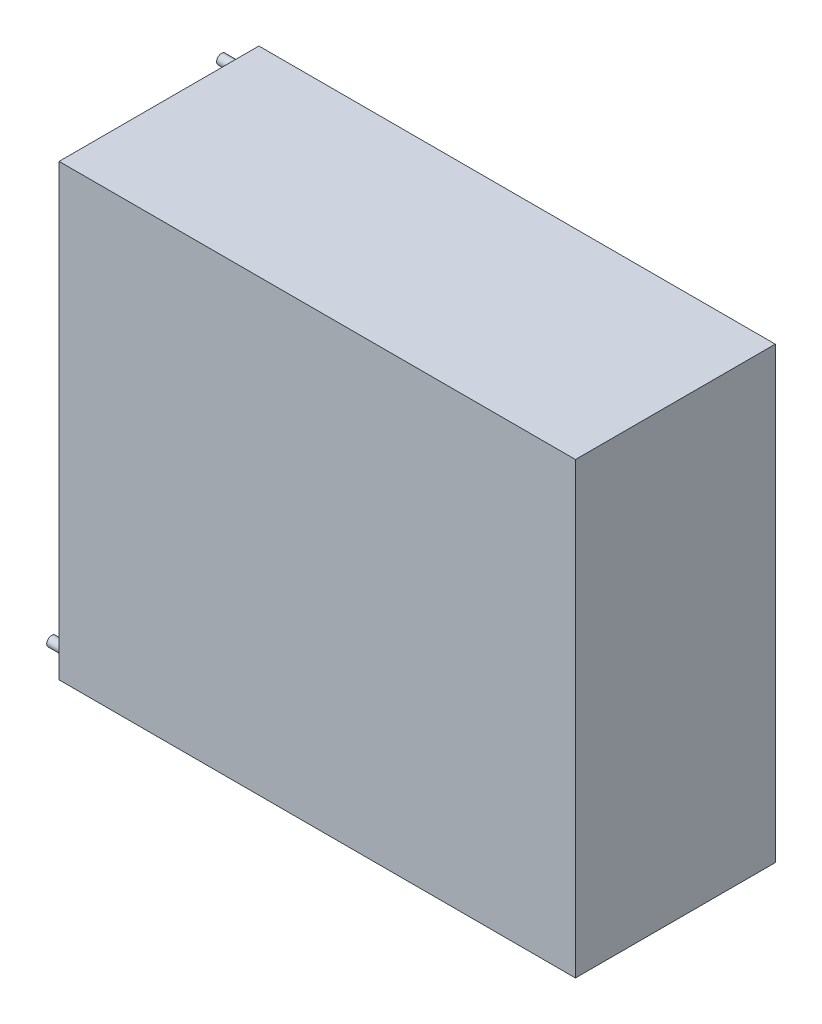
SolidWorks part; units mm, degrees
ref_plane "Alzado" through (0, 0, 0) normal (0, 0, 1) x (1, 0, 0)
ref_plane "Planta" through (0, 0, 0) normal (0, 1, 0) x (1, 0, 0)
ref_plane "Vista lateral" through (0, 0, 0) normal (1, 0, 0) x (0, 0, -1)
sketch "Croquis1" plane through (0, 0, 0) normal (0, 0, 1) x (1, 0, 0)
  line L1 (34.5, -30) -> (-34.5, -30)
  line L2 (34.5, -30) -> (34.5, 30)
  line L3 (34.5, 30) -> (-34.5, 30)
  line L4 (-34.5, -30) -> (-34.5, 30)
  line L5 (34.5, -30) -> (-34.5, 30) construction
  line L6 (34.5, 30) -> (-34.5, -30) construction
  point P0 (0, 0)
  dimension "D1" = 69
  dimension "D2" = 60
extrude "Saliente-Extruir1" add sketch "Croquis1" along normal blind 26.7
sketch "Croquis2" plane through (-34.5, 0, 0) normal (-1, 0, 0) x (0, 0, 1)
  line L0 (26.7, 30) -> (0, 30) construction
  line L1 (0, 30) -> (0, -30) construction
  line L2 (26.7, 30) -> (26.7, -30) construction
  line L3 (26.7, -30) -> (0, -30) construction
  circle A0 centre (24.7, -28) radius 0.65
  circle A1 centre (2, 28) radius 0.65
  dimension "D1" = 1.3
  dimension "D6" = 1.3
  dimension "D2" = 2
  dimension "D3" = 2
  dimension "D4" = 2
  dimension "D5" = 2
extrude "Saliente-Extruir2" add sketch "Croquis2" along normal blind 3
